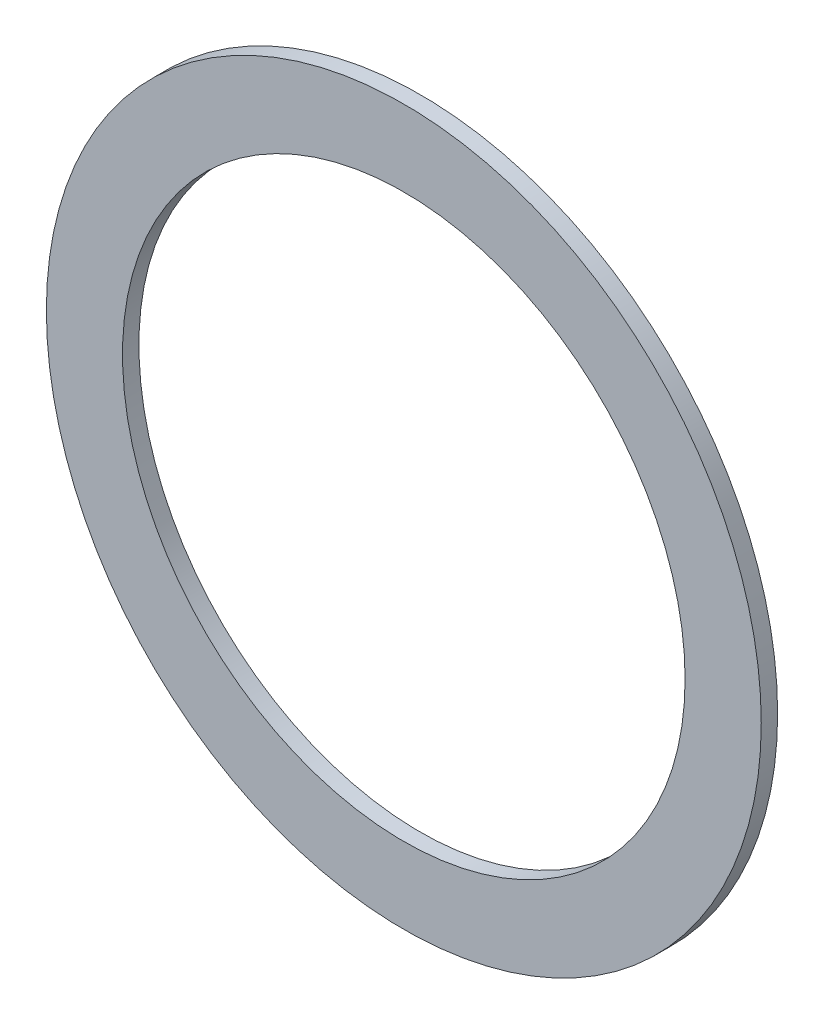
SolidWorks part; units mm, degrees
material "AISI 304"
ref_plane "Front Plane" through (0, 0, 0) normal (0, 0, 1) x (1, 0, 0)
ref_plane "Top Plane" through (0, 0, 0) normal (0, 1, 0) x (1, 0, 0)
ref_plane "Right Plane" through (0, 0, 0) normal (1, 0, 0) x (0, 0, -1)
sketch "Sketch1" plane through (0, 0, 0) normal (0, 0, 1) x (1, 0, 0)
  circle A0 centre (0, 0) radius 8.7249
  circle A1 centre (0, 0) radius 11.0871
  dimension "D1" = 17.4498
  dimension "D2" = 22.1742
extrude "Boss-Extrude1" add sketch "Sketch1" along normal blind 0.508
